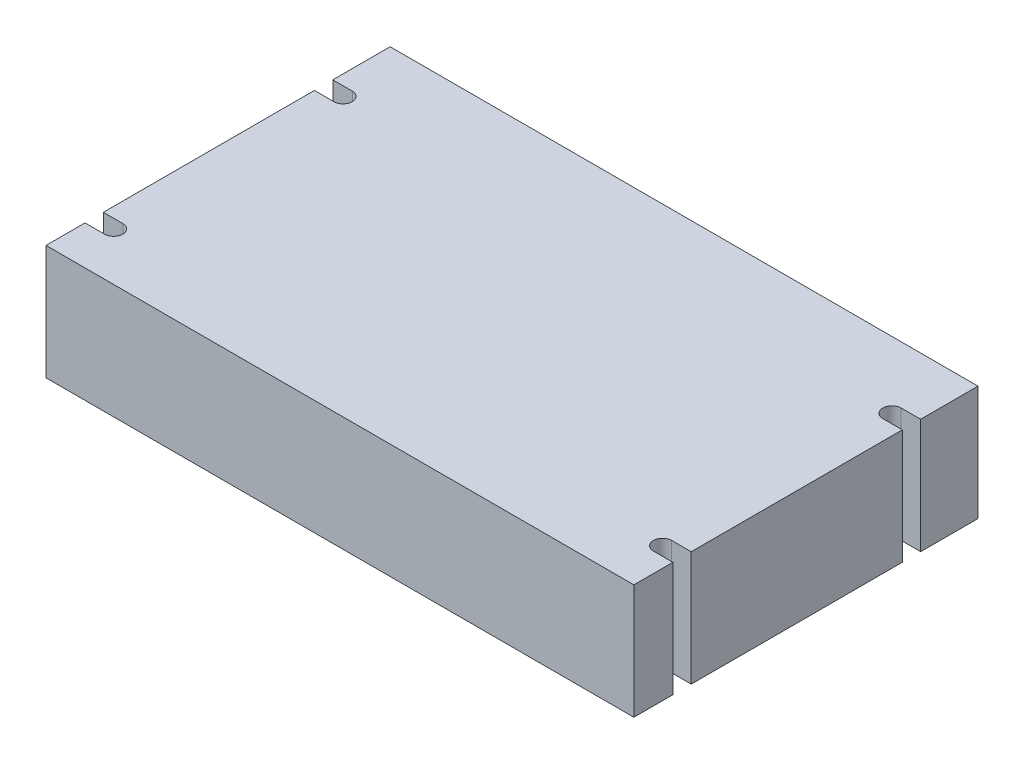
SolidWorks part; units mm, degrees
ref_plane "Front Plane" through (0, 0, 0) normal (0, 0, 1) x (1, 0, 0)
ref_plane "Top Plane" through (0, 0, 0) normal (0, 1, 0) x (1, 0, 0)
ref_plane "Right Plane" through (0, 0, 0) normal (1, 0, 0) x (0, 0, -1)
sketch "Sketch1" plane through (0, 0, 0) normal (0, 1, 0) x (1, 0, 0)
  line L1 (-65.0875, -38.1) -> (65.0875, -38.1)
  line L2 (-65.0875, -38.1) -> (-65.0875, 38.1)
  line L3 (-65.0875, 38.1) -> (65.0875, 38.1)
  line L4 (65.0875, -38.1) -> (65.0875, 38.1)
  line L5 (-65.0875, -38.1) -> (65.0875, 38.1) construction
  line L6 (-65.0875, 38.1) -> (65.0875, -38.1) construction
  point P0 (0, 0)
  dimension "D1" = 130.175
  dimension "D2" = 76.2
extrude "Boss-Extrude1" add sketch "Sketch1" along normal blind 25.4
sketch "Sketch2" plane through (0, 25.4, 0) normal (0, 1, 0) x (1, 0, 0)
  line L0 (-60.7695, 25.4) -> (-65.0875, 25.4)
  line L1 (-65.0875, 38.1) -> (-65.0875, -38.1) construction
  line L2 (-60.7695, 21.336) -> (-65.0875, 21.336)
  line L3 (-65.0875, 21.336) -> (-65.0875, 25.4)
  line L4 (-60.7695, -25.4) -> (-65.0875, -25.4)
  line L5 (-65.0875, -25.4) -> (-65.0875, -29.464)
  line L6 (-65.0875, -29.464) -> (-60.7695, -29.464)
  line L7 (65.0875, 38.1) -> (-65.0875, 38.1) construction
  arc A0 (-60.7695, 21.336) -> (-60.7695, 25.4) centre (-60.7695, 23.368) ccw
  arc A1 (-60.7695, -29.464) -> (-60.7695, -25.4) centre (-60.7695, -27.432) ccw
  point P14 (-58.7375, 23.368)
  point P15 (-58.7375, -27.432)
  dimension "D1" = 4.064
  dimension "D2" = 12.7
  dimension "D3" = 63.5
  dimension "D4" = 6.35
  dimension "D5" = 6.35
extrude "Cut-Extrude1" cut sketch "Sketch2" against normal through all
mirror "Mirror2" about plane through (0, 0, 0) normal (1, 0, 0) of "Cut-Extrude1"
equation "\"D5@Sketch2\"=\"D4@Sketch2\""
